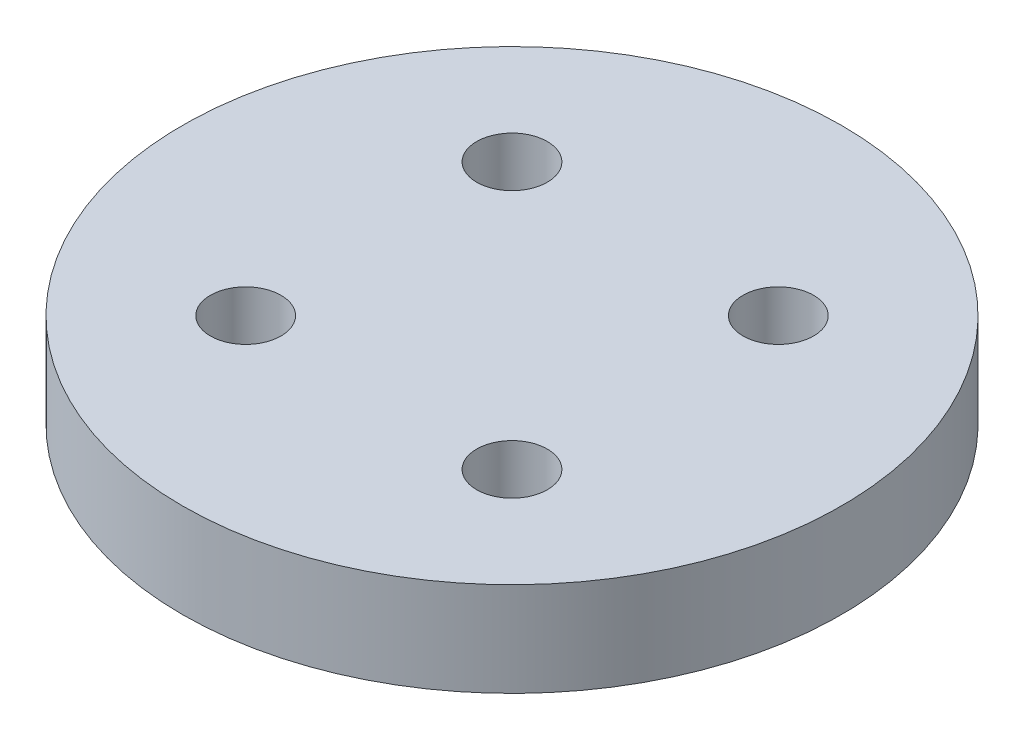
SolidWorks part; units mm, degrees
ref_plane "前视基准面" through (0, 0, 0) normal (0, 0, 1) x (1, 0, 0)
ref_plane "上视基准面" through (0, 0, 0) normal (0, 1, 0) x (1, 0, 0)
ref_plane "右视基准面" through (0, 0, 0) normal (1, 0, 0) x (0, 0, -1)
sketch "草图1" plane through (0, 0, 0) normal (0, 1, 0) x (1, 0, 0)
  line L1 (-5.6569, 5.6569) -> (5.6569, 5.6569) construction
  line L2 (-5.6569, 5.6569) -> (-5.6569, -5.6569) construction
  line L3 (-5.6569, -5.6569) -> (5.6569, -5.6569) construction
  line L4 (5.6569, 5.6569) -> (5.6569, -5.6569) construction
  line L5 (-5.6569, 5.6569) -> (5.6569, -5.6569) construction
  line L6 (-5.6569, -5.6569) -> (5.6569, 5.6569) construction
  circle A0 centre (0, 0) radius 14
  circle A1 centre (-5.6569, 5.6569) radius 1.5
  circle A2 centre (5.6569, 5.6569) radius 1.5
  circle A3 centre (5.6569, -5.6569) radius 1.5
  circle A4 centre (-5.6569, -5.6569) radius 1.5
  point P11 (6.3812, 6.3812)
  dimension "D1" = 28
  dimension "D3" = 3
  dimension "D2" = 16
extrude "凸台-拉伸1" add sketch "草图1" along normal blind 4
